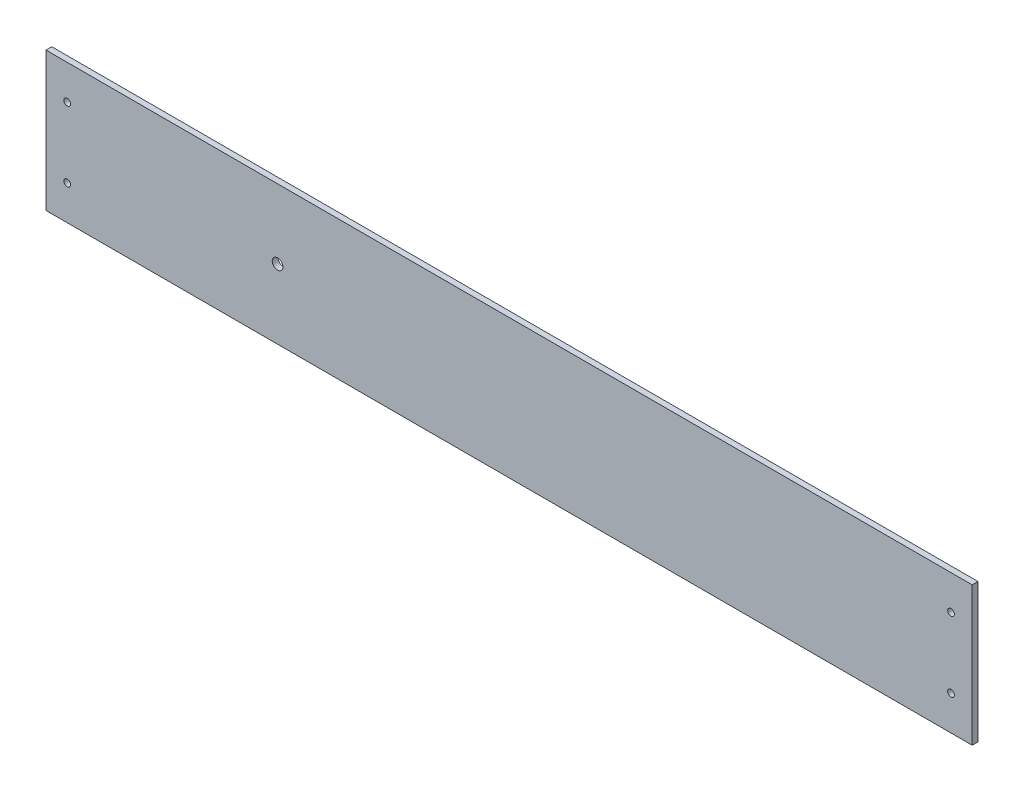
SolidWorks part; units mm, degrees
ref_plane "Front" through (0, 0, 0) normal (0, 0, 1) x (1, 0, 0)
ref_plane "Top" through (0, 0, 0) normal (0, 1, 0) x (1, 0, 0)
ref_plane "Right" through (0, 0, 0) normal (1, 0, 0) x (0, 0, -1)
sketch "Sketch1" plane through (0, 0, 0) normal (0, 0, 1) x (1, 0, 0)
  line L1 (0, 0) -> (508, 0)
  line L2 (0, 0) -> (0, 76.2)
  line L3 (0, 76.2) -> (508, 76.2)
  line L4 (508, 0) -> (508, 76.2)
  dimension "D1" = 508
  dimension "D2" = 76.2
extrude "basic_plank" add sketch "Sketch1" along normal blind 3.175
sketch "Sketch4" plane through (0, 0, 3.175) normal (0, 0, 1) x (1, 0, 0)
  line L1 (0, 76.2) -> (0, 0) construction
  line L2 (508, 76.2) -> (0, 76.2) construction
  circle A0 centre (127, 38.1) radius 2.921
  dimension "D1" = 5.842
  dimension "D2" = 127
  dimension "D3" = 38.1
extrude "through_tripod" cut sketch "Sketch4" against normal through all
sketch "Sketch5" plane through (0, 0, 3.175) normal (0, 0, 1) x (1, 0, 0)
  line L0 (508, 76.2) -> (0, 76.2) construction
  line L1 (254, 76.2) -> (254, 0) construction
  line L3 (0, 76.2) -> (0, 0) construction
  line L4 (0, 38.1) -> (42.978, 38.1) construction
  circle A0 centre (11.6078, 57.3024) radius 1.8415
  circle A1 centre (11.6078, 18.8976) radius 1.8415
  circle A2 centre (496.3922, 18.8976) radius 1.8415
  circle A3 centre (496.3922, 57.3024) radius 1.8415
  dimension "D1" = 3.683
  dimension "D2" = 18.8976
  dimension "D3" = 11.6078
extrude "bracket holes" cut sketch "Sketch5" against normal through all
